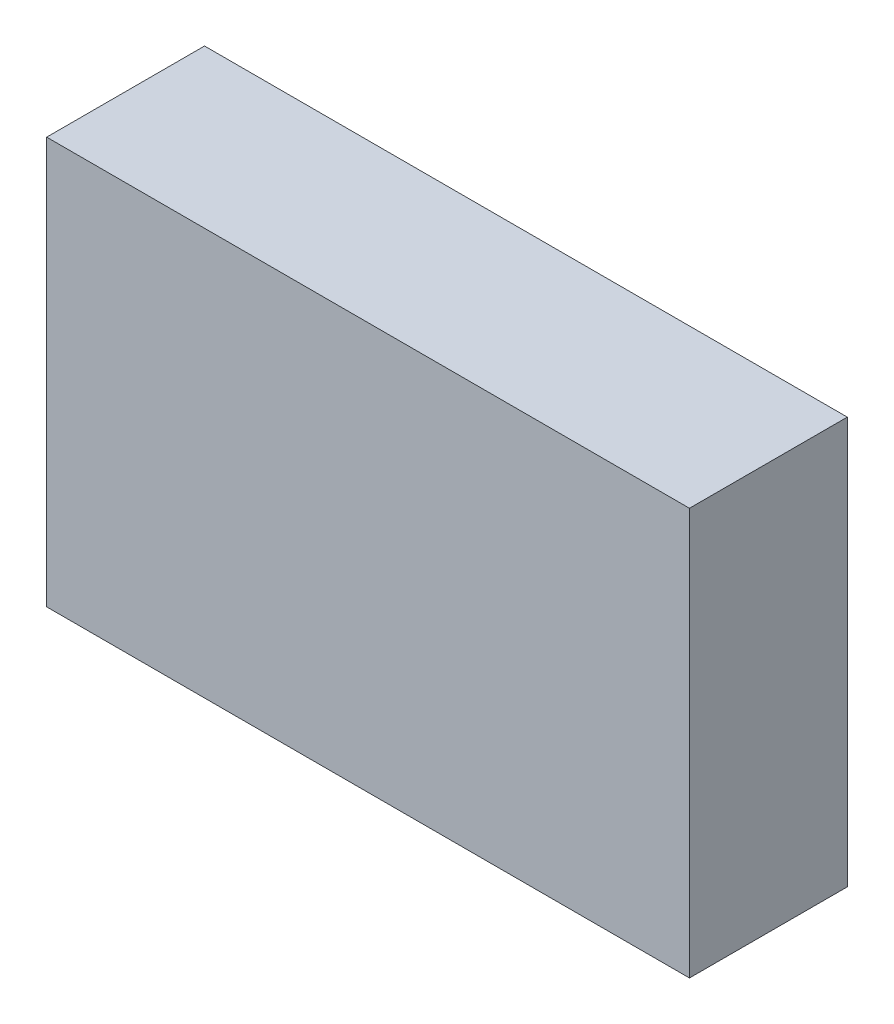
SolidWorks part; units mm, degrees
ref_plane "Front Plane" through (0, 0, 0) normal (0, 0, 1) x (1, 0, 0)
ref_plane "Top Plane" through (0, 0, 0) normal (0, 1, 0) x (1, 0, 0)
ref_plane "Right Plane" through (0, 0, 0) normal (1, 0, 0) x (0, 0, -1)
sketch "Sketch1" plane through (0, 0, 0) normal (0, 0, 1) x (1, 0, 0)
  line L1 (-50.165, 31.75) -> (50.165, 31.75)
  line L2 (-50.165, 31.75) -> (-50.165, -31.75)
  line L3 (-50.165, -31.75) -> (50.165, -31.75)
  line L4 (50.165, 31.75) -> (50.165, -31.75)
  line L5 (-50.165, 31.75) -> (50.165, -31.75) construction
  line L6 (-50.165, -31.75) -> (50.165, 31.75) construction
  point P0 (0, 0)
  dimension "D1" = 63.5
  dimension "D2" = 100.33
extrude "Boss-Extrude1" add sketch "Sketch1" along normal blind 24.638
sketch "Sketch3" plane through (-50.165, 0, 0) normal (-1, 0, 0) x (0, 0, 1)
  line L8 (8.89, 22.86) -> (19.05, 22.86)
  line L9 (8.89, 22.86) -> (8.89, 13.97)
  line L10 (8.89, 13.97) -> (19.05, 13.97)
  line L11 (19.05, 22.86) -> (19.05, 13.97)
  line L12 (8.89, 22.86) -> (19.05, 13.97) construction
  line L13 (8.89, 13.97) -> (19.05, 22.86) construction
  line L14 (0, 31.75) -> (0, -31.75) construction
  line L15 (24.638, 31.75) -> (0, 31.75) construction
  line L17 (5.08, 9.906) -> (19.05, 9.906)
  line L18 (5.08, 9.906) -> (5.08, 3.302)
  line L19 (5.08, 3.302) -> (19.05, 3.302)
  line L20 (19.05, 9.906) -> (19.05, 3.302)
  line L21 (5.08, 9.906) -> (19.05, 3.302) construction
  line L22 (5.08, 3.302) -> (19.05, 9.906) construction
  point P0 (13.97, 18.415)
  point P11 (12.065, 6.604)
  dimension "D1" = 8.89
  dimension "D2" = 8.89
  dimension "D3" = 10.16
  dimension "D4" = 8.89
  dimension "D5" = 4.064
  dimension "D6" = 6.604
  dimension "D7" = 13.97
extrude "Cut-Extrude1" cut sketch "Sketch3" against normal blind 25.4
sketch "Sketch4" plane through (-50.165, 0, 0) normal (-1, 0, 0) x (0, 0, 1)
  line L0 (0, 31.75) -> (0, -31.75) construction
  line L1 (7.112, -6.35) -> (17.526, -6.35)
  line L2 (7.112, -6.35) -> (7.112, -21.59)
  line L3 (7.112, -21.59) -> (17.526, -21.59)
  line L4 (17.526, -6.35) -> (17.526, -21.59)
  line L5 (7.112, -6.35) -> (17.526, -21.59) construction
  line L6 (7.112, -21.59) -> (17.526, -6.35) construction
  line L7 (24.638, -31.75) -> (0, -31.75) construction
  point P0 (12.319, -13.97)
  dimension "D1" = 7.112
  dimension "D2" = 10.16
  dimension "D3" = 10.414
  dimension "D4" = 15.24
extrude "Boss-Extrude2" add sketch "Sketch4" along normal blind 5.08
